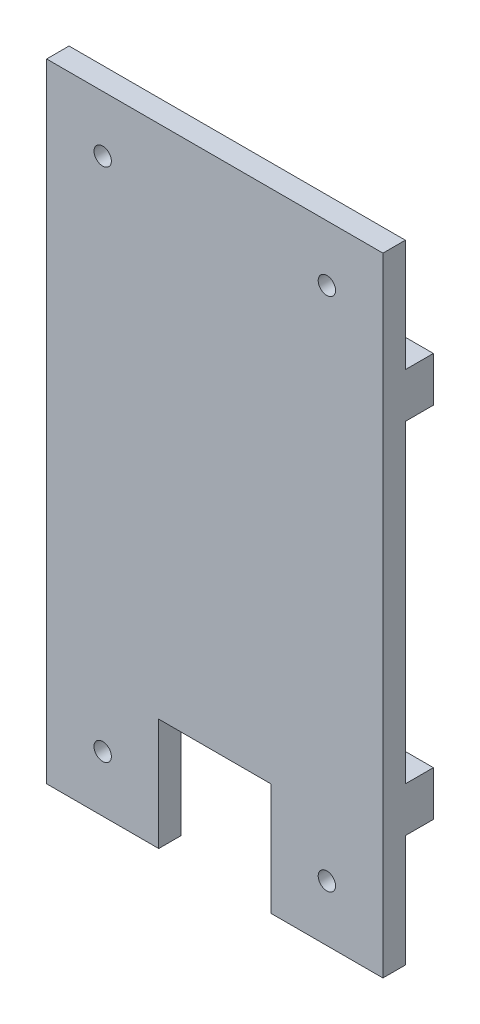
SolidWorks part; units mm, degrees
ref_plane "Front" through (0, 0, 0) normal (0, 0, 1) x (1, 0, 0)
ref_plane "Top" through (0, 0, 0) normal (0, 1, 0) x (1, 0, 0)
ref_plane "Right" through (0, 0, 0) normal (1, 0, 0) x (0, 0, -1)
sketch "Sketch1" plane through (0, 0, 0) normal (0, 0, 1) x (1, 0, 0)
  line L1 (-30, -56) -> (30, -56)
  line L2 (-30, -56) -> (-30, 56)
  line L3 (-30, 56) -> (30, 56)
  line L4 (30, -56) -> (30, 56)
  line L5 (-30, -56) -> (30, 56) construction
  line L6 (-30, 56) -> (30, -56) construction
  line L7 (-10, -56) -> (10, -56)
  line L8 (-10, -56) -> (-10, -36)
  line L9 (-10, -36) -> (10, -36)
  line L10 (10, -56) -> (10, -36)
  line L11 (-10, -56) -> (10, -36) construction
  line L12 (-10, -36) -> (10, -56) construction
  circle A0 centre (-20, -46) radius 1.55
  circle A1 centre (20, -46) radius 1.55
  circle A2 centre (-20, 46) radius 1.55
  circle A3 centre (20, 46) radius 1.55
  point P0 (0, 0)
  point P10 (0, -46)
  dimension "D4" = 3.1
  dimension "D5" = 3.1
  dimension "D6" = 10
  dimension "D7" = 10
  dimension "D8" = 10
  dimension "D9" = 3.1
  dimension "D10" = 3.1
  dimension "D11" = 10
  dimension "D1" = 112
  dimension "D2" = 60
  dimension "D3" = 20
extrude "Boss-Extrude1" add sketch "Sketch1" along normal blind 4 contours L10 L1 L4 L3 L2 L8 L9 A3 A2 A1 A0
sketch "Sketch2" plane through (0, 0, 0) normal (0, 0, -1) x (-1, 0, 0)
  line L0 (-30, -56) -> (-30, 56) construction
  line L1 (-30, 36) -> (30, 36)
  line L2 (-30, 36) -> (-30, -36)
  line L3 (-30, -36) -> (30, -36)
  line L4 (30, 36) -> (30, -36)
  line L5 (-30, 36) -> (30, -36) construction
  line L6 (-30, -36) -> (30, 36) construction
  line L7 (30, -56) -> (30, 56) construction
  line L8 (30, 56) -> (-30, 56) construction
  line L9 (-10, -56) -> (-30, -56) construction
  line L10 (-30, 28) -> (30, 28)
  line L11 (-30, -28) -> (30, -28)
  point P4 (0, 0)
  line M10 (-10, -36) -> (10, -36)
  line M13 (30, -56) -> (30, 56)
  line M15 (-30, 56) -> (-30, -56)
  dimension "D1" = 20
  dimension "D2" = 20
  dimension "D3" = 8
  dimension "D4" = 8
extrude "Boss-Extrude2" add sketch "Sketch2" along normal blind 5 contours L10 L4 L1 M15 | L11 L3 M15 M10 M13
